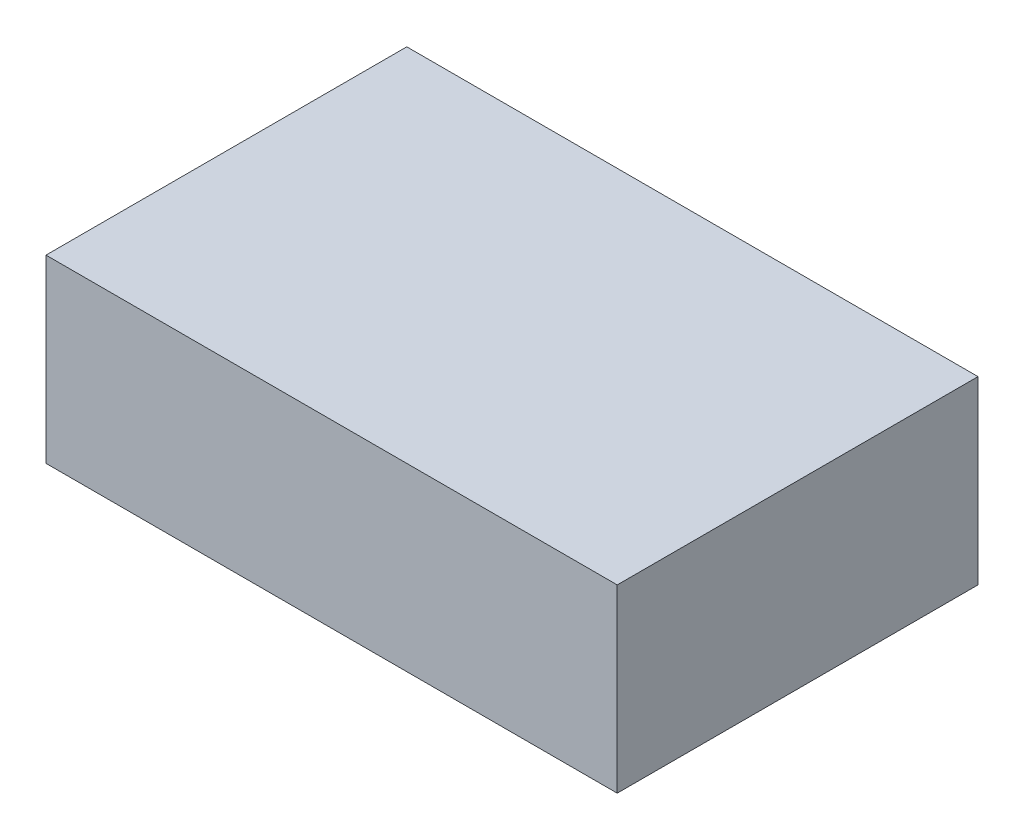
SolidWorks part; units mm, degrees
ref_plane "Płaszczyzna przednia" through (0, 0, 0) normal (0, 0, 1) x (1, 0, 0)
ref_plane "Płaszczyzna górna" through (0, 0, 0) normal (0, 1, 0) x (1, 0, 0)
ref_plane "Płaszczyzna prawa" through (0, 0, 0) normal (1, 0, 0) x (0, 0, -1)
sketch "Szkic1" plane through (0, 0, 0) normal (0, 1, 0) x (1, 0, 0)
  line L1 (-190, -120) -> (190, -120)
  line L2 (-190, -120) -> (-190, 120)
  line L3 (-190, 120) -> (190, 120)
  line L4 (190, -120) -> (190, 120)
  line L5 (-190, -120) -> (190, 120) construction
  line L6 (-190, 120) -> (190, -120) construction
  point P0 (0, 0)
  dimension "D1" = 240
  dimension "D2" = 380
extrude "Dodanie-wyciągnięcie1" add sketch "Szkic1" along normal blind 120
